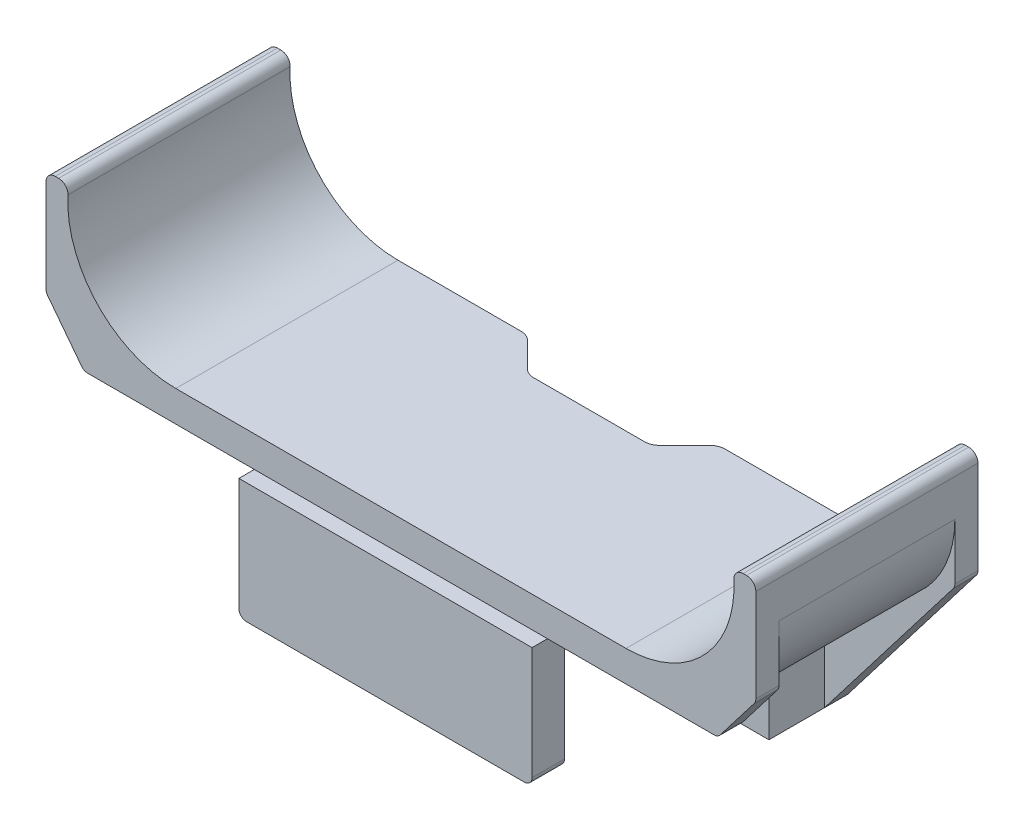
SolidWorks part; units mm, degrees
ref_plane "前视基准面" through (0, 0, 0) normal (0, 0, 1) x (1, 0, 0)
ref_plane "上视基准面" through (0, 0, 0) normal (0, 1, 0) x (1, 0, 0)
ref_plane "右视基准面" through (0, 0, 0) normal (1, 0, 0) x (0, 0, -1)
sketch "草图1" plane through (0, 0, 0) normal (0, 0, 1) x (1, 0, 0)
  line L0 (0, 0) -> (0, 50.9298) construction
  line L1 (16, 0) -> (-16, 0)
  line L2 (-23, 7) -> (-23, 9.4)
  line L3 (-22.4, 10) -> (-22.1792, 10)
  line L5 (-14.5898, 2) -> (14.5898, 2)
  line L7 (22.4, 10) -> (22.1792, 10)
  line L8 (23, 7) -> (23, 9.4)
  arc A0 (-16, 0) -> (-23, 7) centre (-16, 7) cw
  arc A1 (-21.5801, 9.3684) -> (-14.5898, 2) centre (-14.5898, 9) ccw
  arc A2 (-22.1792, 10) -> (-21.5801, 9.3684) centre (-22.1792, 9.4) cw
  arc A3 (-23, 9.4) -> (-22.4, 10) centre (-22.4, 9.4) cw
  arc A4 (23, 9.4) -> (22.4, 10) centre (22.4, 9.4) ccw
  arc A5 (22.1792, 10) -> (21.5801, 9.3684) centre (22.1792, 9.4) ccw
  arc A6 (21.5801, 9.3684) -> (14.5898, 2) centre (14.5898, 9) cw
  arc A7 (16, 0) -> (23, 7) centre (16, 7) ccw
  point P10 (-23, 0)
  point P13 (-18, 2)
  point P16 (-21.8, 10)
  point P19 (-23, 10)
  point P32 (0, 2)
  dimension "D6" = 7
  dimension "D7" = 7
  dimension "D8" = 0.6
  dimension "D1" = 23
  dimension "D2" = 10
  dimension "D3" = 2
  dimension "D4" = 1.2
  dimension "D5" = 18
extrude "凸台-拉伸1" add sketch "草图1" along normal blind 14.4
sketch "草图2" plane through (0, 2, 0) normal (0, 1, 0) x (1, 0, 0)
  line L0 (0, 0) -> (0, -14.4) construction
  line L1 (14.5898, -14.4) -> (-14.5898, -14.4) construction
  line L2 (4, -2.2) -> (-4, -2.2)
  line L3 (6.2, 0) -> (4, -2.2)
  line L4 (14.5898, 0) -> (-14.5898, 0) construction
  line L5 (-6.2, 0) -> (6.2, 0)
  line L6 (-6.2, 0) -> (-4, -2.2)
  point P12 (0, -2.2)
  dimension "D1" = 8
  dimension "D2" = 2.2
  dimension "D3" = 2.2
extrude "切除-拉伸1" cut sketch "草图2" against normal up to next
sketch "草图3" plane through (0, 0, 0) normal (0, 0, 1) x (1, 0, 0)
  line L0 (0, 2) -> (0, -9.0597) construction
  line L1 (14.5898, 2) -> (-14.5898, 2) construction
  line L2 (-7.75, 2) -> (-7.75, -7.8)
  line L3 (-7.75, -7.8) -> (-14.55, -7.8)
  line L4 (-23, 8.2) -> (-22.0471, 8.2)
  line L5 (-23, 8.2) -> (-23, 3.2)
  line L6 (-23, 9.4) -> (-23, 7) construction
  line L7 (-23, 3.2) -> (-14.55, -7.8)
  line L8 (-22.0471, 8.2) -> (-19.5566, 2.6461)
  line L9 (-19.5566, 2.6461) -> (-16.8355, 2)
  line L10 (-16.8355, 2) -> (-7.75, 2)
  line L11 (16.8355, 2) -> (7.75, 2)
  line L12 (19.5566, 2.6461) -> (16.8355, 2)
  line L13 (22.0471, 8.2) -> (19.5566, 2.6461)
  line L14 (23, 3.2) -> (14.55, -7.8)
  line L15 (23, 8.2) -> (23, 3.2)
  line L16 (23, 8.2) -> (22.0471, 8.2)
  line L17 (7.75, -7.8) -> (14.55, -7.8)
  line L18 (7.75, 2) -> (7.75, -7.8)
  dimension "D1" = 9.8
  dimension "D2" = 7.75
  dimension "D3" = 6.8
  dimension "D4" = 5
extrude "凸台-拉伸2" add sketch "草图3" along normal blind 1.5
sketch "草图4" plane through (0, 0, 0) normal (0, -1, 0) x (1, 0, 0)
  line L0 (-7.75, 0) -> (-7.75, 1.5) construction
  line L1 (-14.55, 5.1) -> (-7.75, 5.1)
  line L2 (-14.55, 5.1) -> (-14.55, 1.5)
  line L3 (-14.55, 1.5) -> (-7.75, 1.5)
  line L4 (-7.75, 5.1) -> (-7.75, 1.5)
  line L5 (-14.55, 0) -> (-7.75, 0) construction
  line L6 (0, 0) -> (0, 14.4) construction
  line L7 (-16, 14.4) -> (16, 14.4) construction
  line L8 (7.75, 5.1) -> (7.75, 1.5)
  line L9 (14.55, 1.5) -> (7.75, 1.5)
  line L10 (14.55, 5.1) -> (14.55, 1.5)
  line L11 (14.55, 5.1) -> (7.75, 5.1)
  line L12 (-14.55, 1.5) -> (-7.75, 1.5) construction
  dimension "D1" = 5.1
extrude "凸台-拉伸3" add sketch "草图4" along normal up to surface (7.8 mm away) up to face at (-11.15, -7.8, 0.75)
sketch "草图5" plane through (0, 0, 0) normal (0, -1, 0) x (1, 0, 0)
  line L0 (0, 13.3) -> (0, 0) construction
  line L1 (-9.5, 15.4) -> (9.5, 15.4)
  line L2 (-9.5, 15.4) -> (-9.5, 13.3)
  line L3 (-9.5, 13.3) -> (9.5, 13.3)
  line L4 (9.5, 15.4) -> (9.5, 13.3)
  line L5 (-16, 14.4) -> (16, 14.4) construction
  dimension "D1" = 2.1
  dimension "D2" = 1
  dimension "D3" = 19
extrude "凸台-拉伸4" add sketch "草图5" along normal up to surface (7.8 mm away) up to face at (-11.83, -7.8, 2.34)
sketch "草图6" plane through (0, 0, 14.4) normal (0, 0, 1) x (1, 0, 0)
  line L0 (-7.75, 0) -> (-20.5418, 0)
  line L1 (0, 2) -> (0, -9.0597) construction
  line L2 (0, 2) -> (0, -9.0597) construction
  line L3 (7.75, 0) -> (20.5418, 0)
  line L8 (-7.75, -7.8) -> (-7.75, 2)
  line L9 (-14.55, -7.8) -> (-7.75, -7.8)
  line L10 (-23, 3.2) -> (-14.55, -7.8)
  line L11 (-23, 8.2) -> (-23, 3.2)
  line L12 (-22.0471, 8.2) -> (-23, 8.2)
  line L13 (-19.5566, 2.6461) -> (-22.0471, 8.2)
  line L14 (-16.8355, 2) -> (-19.5566, 2.6461)
  line L15 (-7.75, 2) -> (-16.8355, 2)
  line L16 (-7.75, 0) -> (-7.75, 2)
  line L18 (-23, 3.2) -> (-20.5418, 0)
  line L19 (-23, 8.2) -> (-23, 3.2)
  line L20 (-22.0471, 8.2) -> (-23, 8.2)
  line L21 (-19.5566, 2.6461) -> (-22.0471, 8.2)
  line L22 (-16.8355, 2) -> (-19.5566, 2.6461)
  line L23 (-7.75, 2) -> (-16.8355, 2)
  line L24 (16.8355, 2) -> (7.75, 2)
  line L25 (19.5566, 2.6461) -> (16.8355, 2)
  line L26 (22.0471, 8.2) -> (19.5566, 2.6461)
  line L27 (23, 8.2) -> (22.0471, 8.2)
  line L28 (23, 3.2) -> (23, 8.2)
  line L29 (14.55, -7.8) -> (23, 3.2)
  line L30 (7.75, -7.8) -> (14.55, -7.8)
  line L31 (7.75, 2) -> (7.75, -7.8)
  line L32 (16.8355, 2) -> (7.75, 2)
  line L33 (19.5566, 2.6461) -> (16.8355, 2)
  line L34 (22.0471, 8.2) -> (19.5566, 2.6461)
  line L35 (23, 8.2) -> (22.0471, 8.2)
  line L36 (23, 3.2) -> (23, 8.2)
  line L37 (20.5418, 0) -> (23, 3.2)
  line L39 (7.75, 2) -> (7.75, 0)
  dimension "D1" = 0
  dimension "D2" = 0
extrude "凸台-拉伸5" add sketch "草图6" against normal blind 1.5
hole_wizard "M3 螺纹孔1" positions "草图8" profile "草图7" tap size "M3" standard "Gb"
sketch "草图8" plane through (0, -7.8, 0) normal (0, -1, 0) x (-1, 0, 0)
  line L0 (-11.15, 0) -> (-11.15, -5.1) construction
  line L1 (-7.75, 0) -> (-14.55, 0) construction
  line L2 (-14.55, -5.1) -> (-7.75, -5.1) construction
  line L4 (0, 0) -> (0, -10.805) construction
  line L6 (11.15, 0) -> (11.15, -5.1) construction
  point P0 (-11.15, -2.55)
  point P19 (11.15, -2.55)
  dimension "D1" = 22.3
sketch "草图7" plane through (11.15, -7.8, 2.55) normal (1, 0, 0) x (0, 0, -1)
  line L0 (0, 0) -> (0, 7.2511)
  line L1 (0, 7.2511) -> (1.25, 6.5)
  line L2 (1.25, 6.5) -> (1.25, 0)
  line L5 (1.25, 0) -> (0, 0)
  line L10 (0, 7.2511) -> (-1.25, 6.5) construction
  line L11 (0, -6.35) -> (0, 107.95) construction
  dimension "螺纹孔钻头直径" = 2.5
  dimension "螺纹孔钻头深度" = 6.5
  dimension "导头角度" = 118
cosmetic thread "孔螺蚊线1" parameters "D1"=4, "D2"=3
cosmetic thread "孔螺蚊线2" parameters "D1"=4, "D2"=3
fillet "圆角1" radius 0.5 8 edges at (-23, 3.2, 13.65) (23, 3.2, 13.65) (-20.5418, 0, 13.65) (20.5418, 0, 13.65) (-9.5, -7.8, 14.35) (9.5, -7.8, 14.35) (-23, 3.2, 0.75) (23, 3.2, 0.75)
fillet "圆角2" radius 1 4 edges at (6.2, 1, 0) (-6.2, 1, 0) (-4, 1, 2.2) (4, 1, 2.2)
